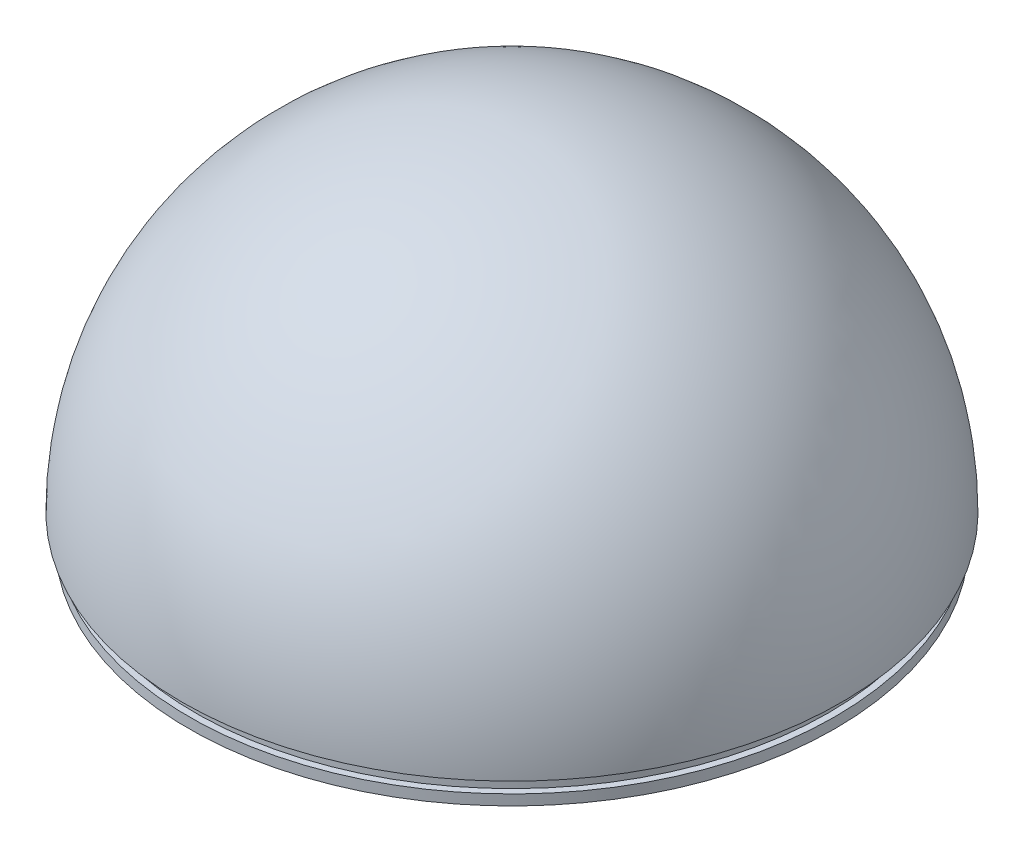
SolidWorks part; units mm, degrees
ref_plane "Front Plane" through (0, 0, 0) normal (0, 0, 1) x (1, 0, 0)
ref_plane "Top Plane" through (0, 0, 0) normal (0, 1, 0) x (1, 0, 0)
ref_plane "Right Plane" through (0, 0, 0) normal (1, 0, 0) x (0, 0, -1)
sketch "Sketch1" plane through (0, 0, 0) normal (0, 1, 0) x (1, 0, 0)
  line L0 (0, 25.25) -> (0, 23.25)
  line L1 (0, -23.25) -> (0, -25.25)
  arc A0 (0, -25.25) -> (0, 25.25) centre (0, 0) ccw
  arc A1 (0, -23.25) -> (0, 23.25) centre (0, 0) ccw
  dimension "D1" = 50.5
  dimension "D2" = 46.5
revolve "Revolve1" add sketch "Sketch1" angle 180 about L1
sketch "Sketch2" plane through (0, 0, 0) normal (0, -1, 0) x (1, 0, 0)
  circle A0 centre (0, 0) radius 23.25
  circle A1 centre (0, 0) radius 22.25
  dimension "D1" = 46.5
  dimension "D2" = 44.5
extrude "Boss-Extrude1" [suppressed] add sketch "Sketch2" along normal blind 2 separate body
sketch "Sketch3" plane through (0, 0, 0) normal (0, -1, 0) x (1, 0, 0)
  circle A0 centre (0, 0) radius 23.25
  circle A1 centre (0, 0) radius 24.75
  dimension "D1" = 46.5
  dimension "D2" = 49.5
extrude "Boss-Extrude2" add sketch "Sketch3" along normal blind 2
sketch "Sketch4" plane through (0, 0, 0) normal (0, -1, 0) x (1, 0, 0)
  circle A0 centre (0, 0) radius 24.25
  circle A1 centre (0, 0) radius 24.75
  dimension "D1" = 49.5
  dimension "D2" = 48.5
extrude "Cut-Extrude1" cut sketch "Sketch4" along normal blind 1.2
